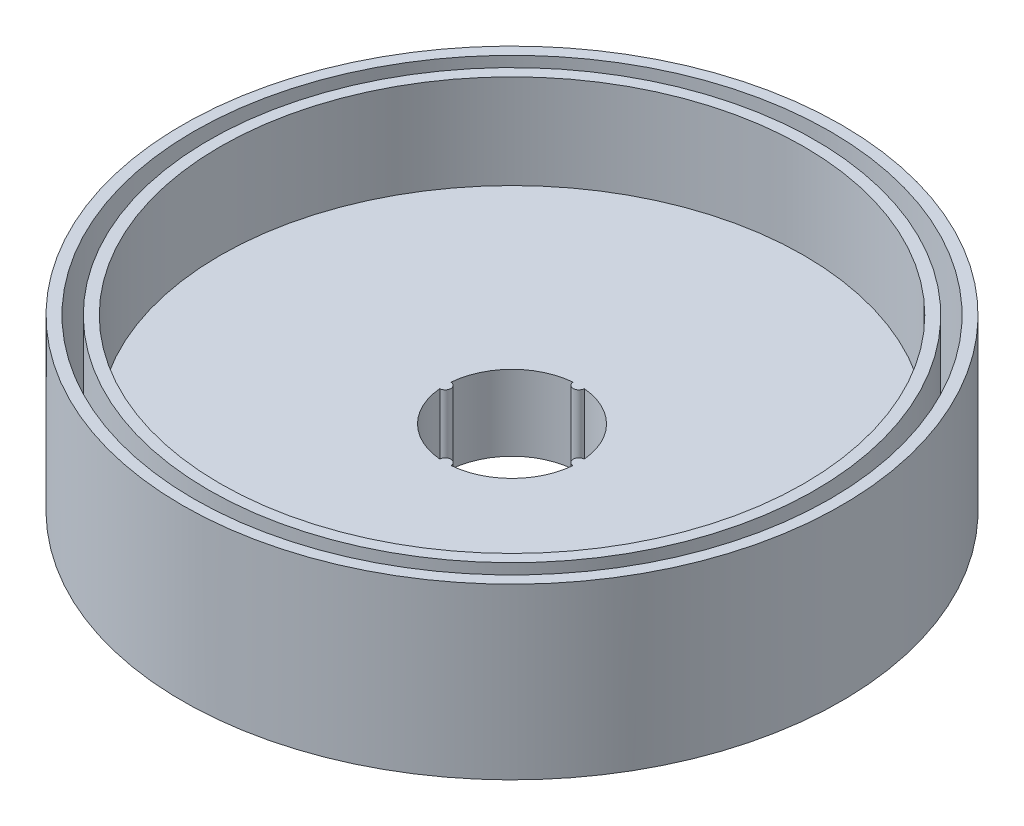
SolidWorks part; units mm, degrees
ref_plane "Front Plane" through (0, 0, 0) normal (0, 0, 1) x (1, 0, 0)
ref_plane "Top Plane" through (0, 0, 0) normal (0, 1, 0) x (1, 0, 0)
ref_plane "Right Plane" through (0, 0, 0) normal (1, 0, 0) x (0, 0, -1)
sketch "Sketch1" plane through (0, 0, 0) normal (0, 1, 0) x (1, 0, 0)
  circle A0 centre (0, 0) radius 17.5
  circle A1 centre (0, 0) radius 15.5
  point P5 (0, 0)
  dimension "D1" = 35
  dimension "D2" = 31
extrude "Boss-Extrude1" add sketch "Sketch1" along normal blind 5
sketch "Sketch3" plane through (0, 0, 0) normal (0, -1, 0) x (1, 0, 0)
  circle A0 centre (0, 0) radius 17.5
  arc A1 (-0.2997, 3.5373) -> (-3.5373, 0.2997) centre (0, 0) ccw
  arc A3 (-3.5373, -0.2997) -> (-3.5373, 0.2997) centre (-3.55, 0) ccw
  arc A4 (-0.2997, 3.5373) -> (0.2997, 3.5373) centre (0, 3.55) ccw
  arc A5 (3.5373, 0.2997) -> (3.5373, -0.2997) centre (3.55, 0) ccw
  arc A6 (0.2997, -3.5373) -> (-0.2997, -3.5373) centre (0, -3.55) ccw
  arc A7 (3.5373, 0.2997) -> (0.2997, 3.5373) centre (0, 0) ccw
  arc A8 (0.2997, -3.5373) -> (3.5373, -0.2997) centre (0, 0) ccw
  arc A9 (-3.5373, -0.2997) -> (-0.2997, -3.5373) centre (0, 0) ccw
  dimension "D1" = 35
  dimension "D2" = 7.1
  dimension "D3" = 0.6
extrude "Boss-Extrude2" add sketch "Sketch3" along normal blind 4
sketch "Sketch2" plane through (0, 5, 0) normal (0, 1, 0) x (1, 0, 0)
  circle A0 centre (0, 0) radius 16.9
  circle A1 centre (0, 0) radius 16.1
  dimension "D1" = 32.2
  dimension "D2" = 0.8
extrude "Cut-Extrude1" cut sketch "Sketch2" against normal blind 8
